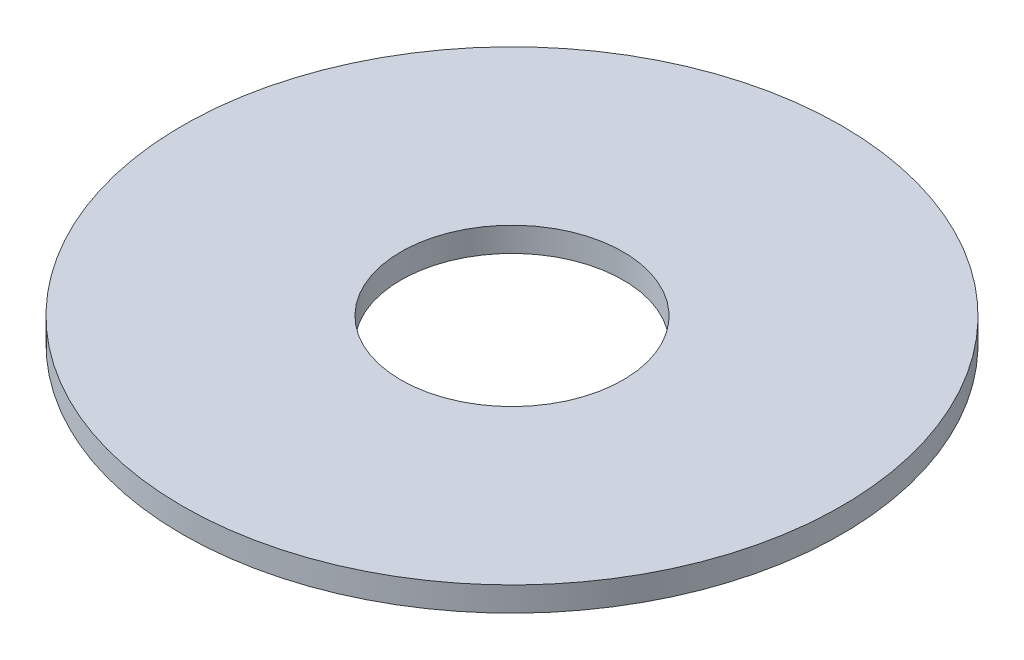
SolidWorks part; units mm, degrees
material "AISI 304"
ref_plane "Front Plane" through (0, 0, 0) normal (0, 0, 1) x (1, 0, 0)
ref_plane "Top Plane" through (0, 0, 0) normal (0, 1, 0) x (1, 0, 0)
ref_plane "Right Plane" through (0, 0, 0) normal (1, 0, 0) x (0, 0, -1)
sketch "Sketch1" plane through (0, 0, 0) normal (0, 1, 0) x (1, 0, 0)
  circle A0 centre (0, 0) radius 7.874
  dimension "OD" = 15.748
extrude "Boss-Extrude1" add sketch "Sketch1" along normal blind 0.5842
sketch "Sketch5" plane through (0, 0.5842, 0) normal (0, 1, 0) x (-1, 0, 0)
  circle A0 centre (0, 0) radius 2.6543
  dimension "ID" = 5.3086
extrude "Cut-Extrude1" cut sketch "Sketch5" against normal through all
